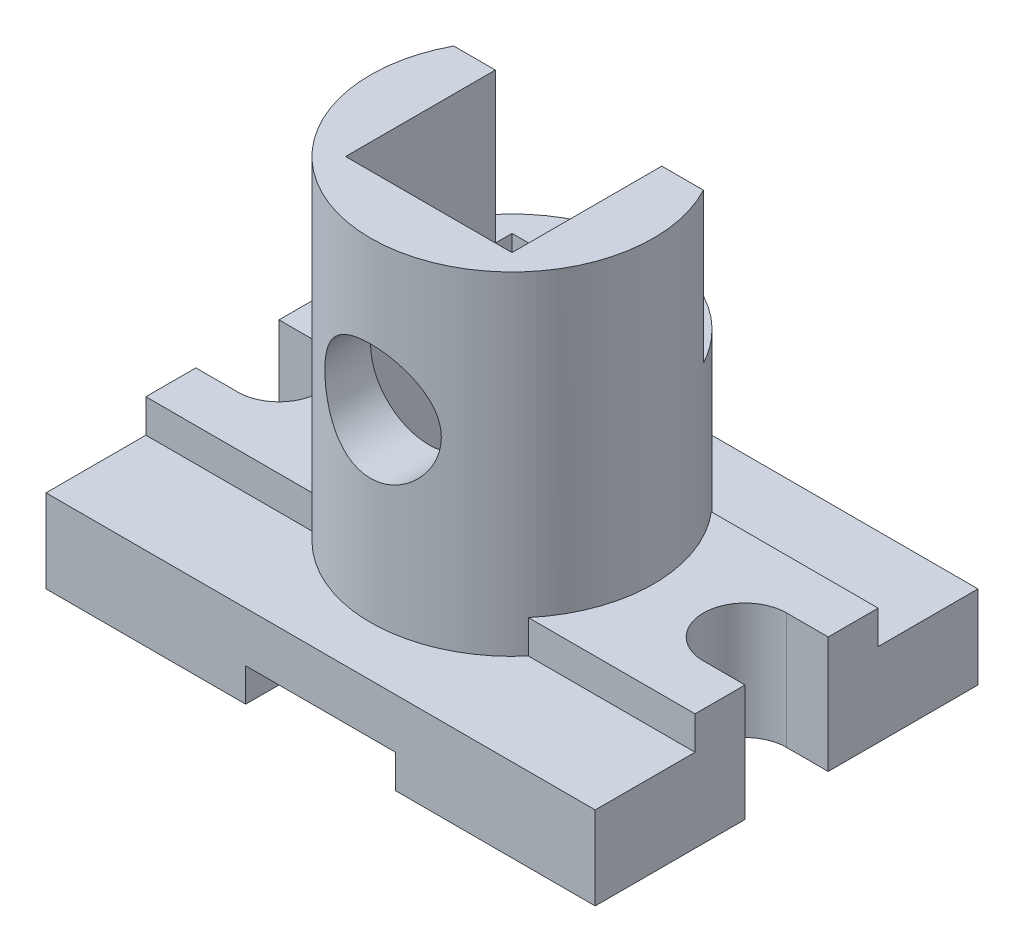
SolidWorks part; units mm, degrees
ref_plane "前视基准面" through (0, 0, 0) normal (0, 0, 1) x (1, 0, 0)
ref_plane "上视基准面" through (0, 0, 0) normal (0, 1, 0) x (1, 0, 0)
ref_plane "右视基准面" through (0, 0, 0) normal (1, 0, 0) x (0, 0, -1)
sketch "草图1" plane through (0, 0, 0) normal (0, 1, 0) x (1, 0, 0)
  line L1 (-33, 23) -> (33, 23)
  line L2 (-33, 23) -> (-33, -23)
  line L3 (-33, -23) -> (33, -23)
  line L4 (33, 23) -> (33, -23)
  dimension "D1" = 66
  dimension "D2" = 46
  dimension "D3" = 23
  dimension "D4" = 33
extrude "凸台-拉伸1" add sketch "草图1" along normal blind 10
sketch "草图2" plane through (0, 10, 0) normal (0, 1, 0) x (1, 0, 0)
  line L0 (-33, 23) -> (-33, -23) construction
  line L1 (33, -23) -> (33, 23) construction
  line L2 (-33, 11) -> (33, 11)
  line L3 (-33, 11) -> (-33, -11)
  line L4 (-33, -11) -> (33, -11)
  line L5 (33, 11) -> (33, -11)
  dimension "D1" = 22
  dimension "D2" = 11
extrude "凸台-拉伸2" add sketch "草图2" along normal blind 4
sketch "草图3" plane through (0, 0, 0) normal (0, 1, 0) x (1, 0, 0)
  circle A0 centre (0, 0) radius 17
  dimension "D1" = 34
extrude "凸台-拉伸3" add sketch "草图3" along normal blind 50
sketch "草图4" plane through (0, 0, 23) normal (0, 0, 1) x (1, 0, 0)
  line L0 (25.3, 0) -> (-25.3, 0) construction
  line L1 (-9, 0) -> (9, 0)
  line L2 (-9, 0) -> (-9, 4)
  line L3 (-9, 4) -> (9, 4)
  line L4 (9, 0) -> (9, 4)
  dimension "D1" = 18
  dimension "D2" = 4
  dimension "D3" = 9
extrude "切除-拉伸1" cut sketch "草图4" against normal through all
sketch "草图5" plane through (0, 14, 0) normal (0, 1, 0) x (1, 0, 0)
  line L0 (-27.5, 0) -> (27.5, 0) construction
  line L1 (-28, 5) -> (-33, 5)
  line L2 (-33, 11) -> (-33, -11) construction
  line L3 (-33, 5) -> (-33, -5)
  line L4 (-33, -5) -> (-28.3831, -4.9853)
  line L5 (0, -25.3) -> (0, 25.3) construction
  line L6 (33, -5) -> (28.3831, -4.9853)
  line L7 (33, 5) -> (33, -5)
  line L8 (28, 5) -> (33, 5)
  arc A0 (-28.3831, -4.9853) -> (-28, 5) centre (-28, 0) ccw
  arc A1 (28.3831, -4.9853) -> (28, 5) centre (28, 0) cw
  dimension "D1" = 10
  dimension "D2" = 28
extrude "切除-拉伸2" cut sketch "草图5" against normal through all
sketch "草图6" plane through (0, 50, 0) normal (0, 1, 0) x (1, 0, 0)
  line L1 (-10, 10) -> (10, 10)
  line L2 (-10, 10) -> (-10, -10)
  line L3 (-10, -10) -> (10, -10)
  line L4 (10, 10) -> (10, -10)
  dimension "D1" = 10
  dimension "D2" = 20
  dimension "D3" = 20
  dimension "D4" = 10
extrude "切除-拉伸3" cut sketch "草图6" against normal through all
sketch "草图7" plane through (0, 50, 0) normal (0, 1, 0) x (1, 0, 0)
  line L0 (-15, 8) -> (-10, 8)
  line L1 (-10, 10) -> (-10, -10) construction
  line L2 (0, -25.3) -> (0, 25.3) construction
  line L4 (15, 8) -> (10, 8)
  line L5 (-27.5, 0) -> (27.5, 0) construction
  line L6 (-10, 8) -> (-10, 10)
  line L7 (-10, 10) -> (10, 10)
  line L8 (10, 10) -> (10, 8)
  circle A0 centre (0, 0) radius 17 construction
  arc A2 (15, 8) -> (-15, 8) centre (0, 0) ccw
  dimension "D1" = 8
extrude "切除-拉伸4" cut sketch "草图7" against normal blind 18
sketch "草图8" plane through (0, 0, 0) normal (0, 0, 1) x (1, 0, 0)
  line L0 (0, -25.3) -> (0, 25.3) construction
  circle A0 centre (0, 32) radius 7
  dimension "D1" = 14
  dimension "D2" = 32
extrude "切除-拉伸5" cut sketch "草图8" along normal through all
sketch "草图9" plane through (0, 0, 0) normal (0, 1, 0) x (1, 0, 0)
  circle A0 centre (0, 0) radius 19
  dimension "D1" = 38
extrude "切除-拉伸6" cut sketch "草图9" along normal blind 6
